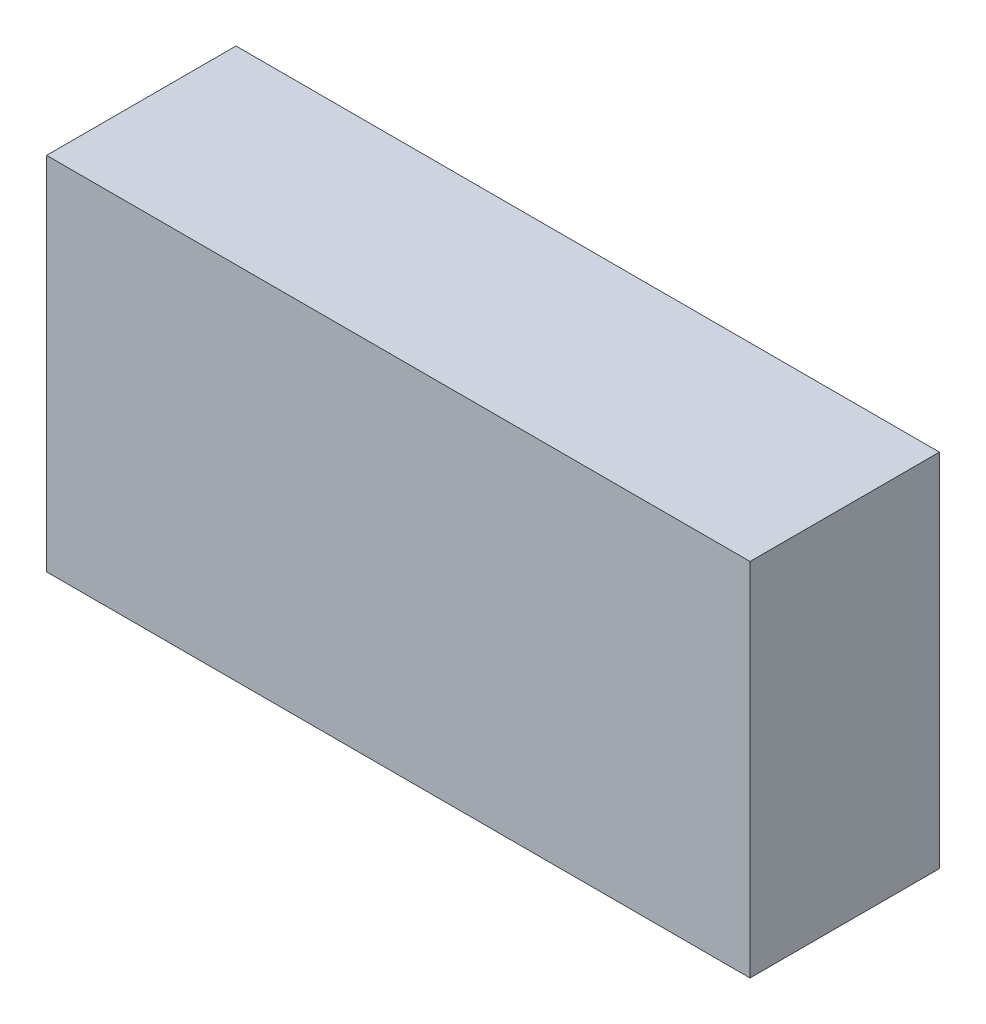
SolidWorks part; units mm, degrees
ref_plane "前视基准面" through (0, 0, 0) normal (0, 0, 1) x (1, 0, 0)
ref_plane "上视基准面" through (0, 0, 0) normal (0, 1, 0) x (1, 0, 0)
ref_plane "右视基准面" through (0, 0, 0) normal (1, 0, 0) x (0, 0, -1)
sketch "草图1" plane through (0, 0, 0) normal (0, 0, 1) x (1, 0, 0)
  line L1 (-39, 20) -> (39, 20)
  line L2 (-39, 20) -> (-39, -20)
  line L3 (-39, -20) -> (39, -20)
  line L4 (39, 20) -> (39, -20)
  line L5 (-39, 20) -> (39, -20) construction
  line L6 (-39, -20) -> (39, 20) construction
  point P0 (0, 0)
  dimension "D1" = 78
  dimension "D2" = 40
extrude "凸台-拉伸1" add sketch "草图1" along normal blind 21
